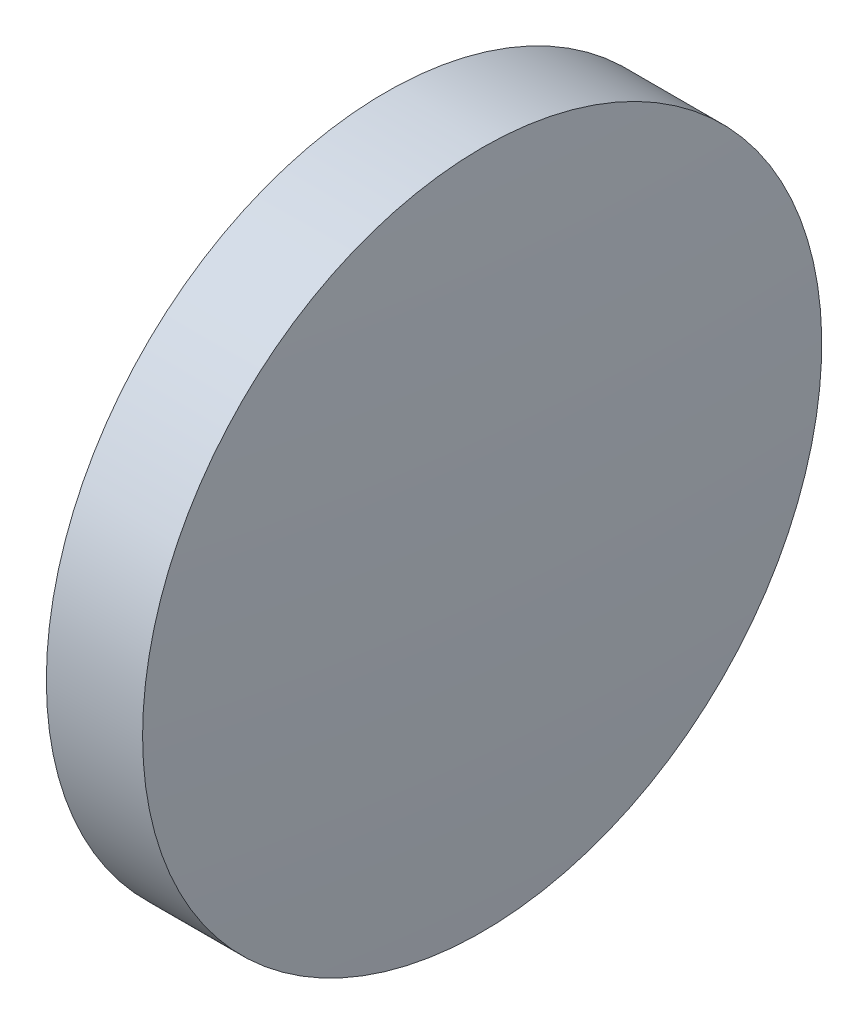
SolidWorks part; units mm, degrees
ref_plane "前视基准面" through (0, 0, 0) normal (0, 0, 1) x (1, 0, 0)
ref_plane "上视基准面" through (0, 0, 0) normal (0, 1, 0) x (1, 0, 0)
ref_plane "右视基准面" through (0, 0, 0) normal (1, 0, 0) x (0, 0, -1)
sketch "草图1" plane through (0, 0, 0) normal (0, 0, 1) x (1, 0, 0)
  line L0 (342.3303, 151.8396) -> (361.1263, 151.8396) construction
  line L1 (348.0685, 151.8396) -> (348.0685, 164.5396)
  line L2 (352.0685, 151.8396) -> (348.0685, 151.8396)
  line L5 (348.0685, 164.5396) -> (351.6685, 164.5396)
  arc A0 (352.0685, 151.8396) -> (351.6685, 164.5396) centre (150.256, 151.8396) ccw
revolve "旋转1" add sketch "草图1" angle 360 about L0
